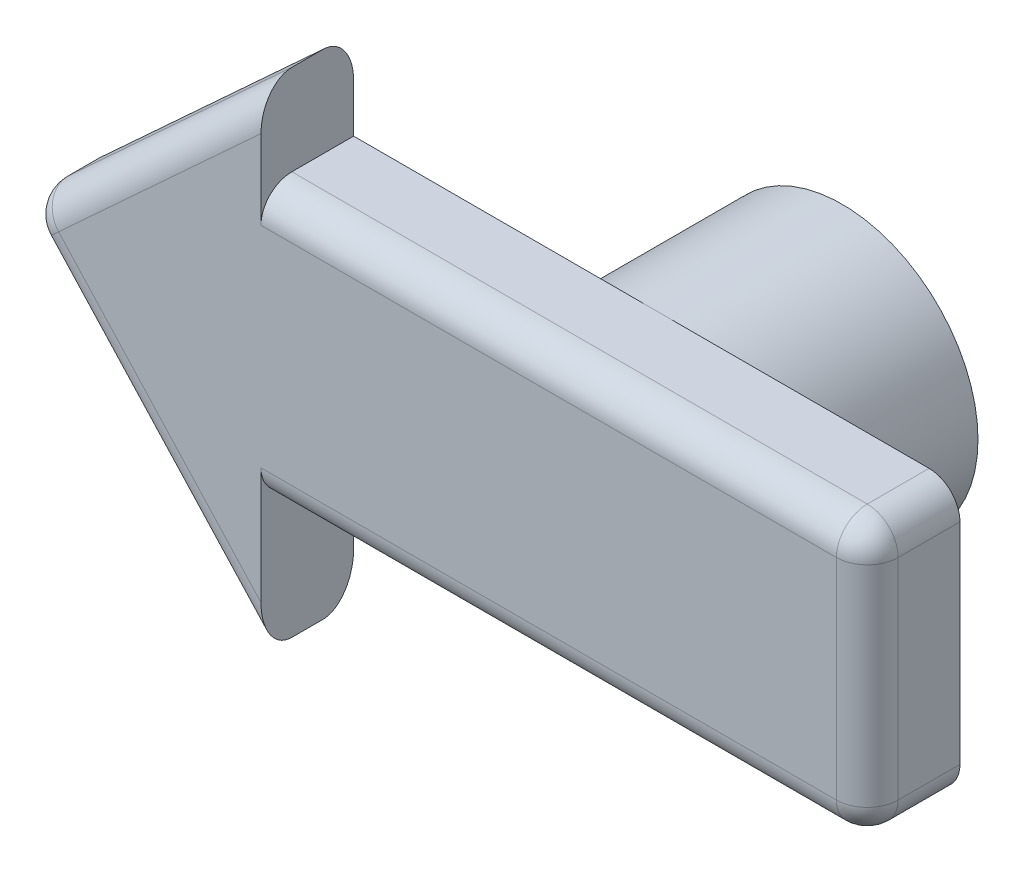
SolidWorks part; units mm, degrees
ref_plane "Front Plane" through (0, 0, 0) normal (0, 0, 1) x (1, 0, 0)
ref_plane "Top Plane" through (0, 0, 0) normal (0, 1, 0) x (1, 0, 0)
ref_plane "Right Plane" through (0, 0, 0) normal (1, 0, 0) x (0, 0, -1)
sketch "Sketch1" plane through (0, 0, 0) normal (0, 0, 1) x (1, 0, 0)
  circle A0 centre (0, -3.7) radius 3.1
  circle A1 centre (0, -3.7) radius 3 construction
  circle A2 centre (0, -3.7) radius 4.4
  dimension "D1" = 0.1
  dimension "D2" = 1.3
extrude "Boss-Extrude1" add sketch "Sketch1" against normal blind 6
sketch "Sketch2" plane through (0, 0, 0) normal (0, 0, 1) x (1, 0, 0)
  line L0 (9.8152, -8.1) -> (9.8152, 0.7)
  line L1 (9.8152, -8.1) -> (-9.8152, -8.1)
  line L2 (9.8152, 0.7) -> (-9.8152, 0.7)
  line L3 (-9.8152, -8.1) -> (-9.8152, 0.7) construction
  line L4 (9.8152, -8.1) -> (-9.8152, 0.7) construction
  line L5 (9.8152, 0.7) -> (-9.8152, -8.1) construction
  line L6 (-9.8152, -8.1) -> (-9.8152, -12.3548)
  line L7 (-9.8152, -12.3548) -> (-17.7797, -3.7)
  line L8 (-17.7797, -3.7) -> (-9.8152, 3.6292)
  line L9 (-9.8152, 3.6292) -> (-9.8152, 0.7)
  point P1 (0, -3.7)
extrude "Boss-Extrude2" add sketch "Sketch2" along normal blind 3
fillet "Fillet1" radius 1 10 edges at (-13.7974, -0.0354, 3) (0, 0.7, 3) (9.8152, -3.7, 3) (0, -8.1, 3) (-13.7974, -8.0274, 3) (-13.7974, -0.0354, 0) (-17.7797, -3.7, 1.5) (-13.7974, -8.0274, 0) (9.8152, 0.7, 1.5) (9.8152, -8.1, 1.5)
